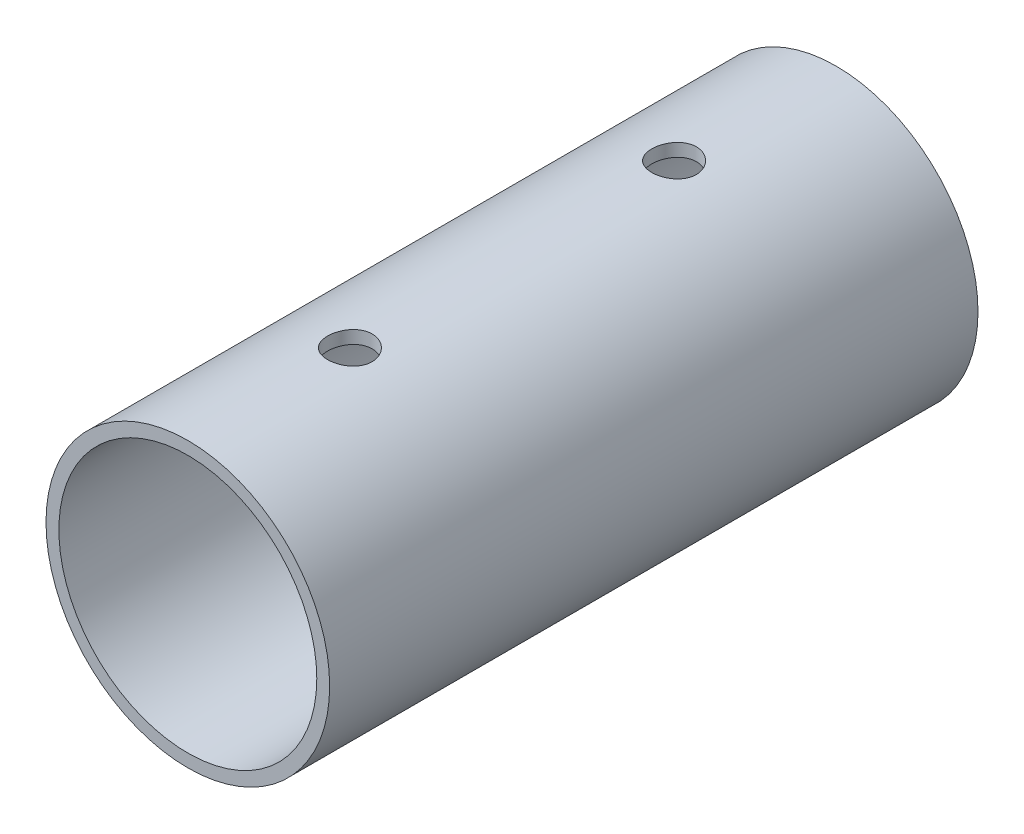
SolidWorks part; units mm, degrees
ref_plane "Front Plane" through (0, 0, 0) normal (0, 0, 1) x (1, 0, 0)
ref_plane "Top Plane" through (0, 0, 0) normal (0, 1, 0) x (1, 0, 0)
ref_plane "Right Plane" through (0, 0, 0) normal (1, 0, 0) x (0, 0, -1)
sketch "Sketch1" plane through (0, 0, 0) normal (0, 0, 1) x (1, 0, 0)
  circle A0 centre (0, 0) radius 15.9125
  circle A1 centre (0, 0) radius 17.5
  dimension "D1" = 35
  dimension "D2" = 31.825
extrude "Boss-Extrude1" add sketch "Sketch1" along normal mid plane 80
sketch "Sketch3" plane through (0, 0, 0) normal (0, 1, 0) x (1, 0, 0)
  line L0 (0, 40) -> (0, 20) construction
  line L1 (17.5, 40) -> (-17.5, 40) construction
  dimension "D1" = 20
hole_wizard "M5 Clearance Hole1" positions "Sketch4" profile "Sketch5" hole size "M5" standard "ANSI Metric"
sketch "Sketch4" plane through (0, 0, 0) normal (0, 1, 0) x (1, 0, 0)
  point P0 (0, 20)
sketch "Sketch5" plane through (0, 0, -20) normal (1, 0, 0) x (0, 0, -1)
  line L0 (0, 0) -> (0, 17.5)
  line L1 (0, 17.5) -> (2.75, 17.5)
  line L2 (2.75, 17.5) -> (2.75, 0)
  line L5 (2.75, 0) -> (0, 0)
  line L11 (0, -6.35) -> (0, 107.95) construction
  dimension "Thru Hole Dia." = 5.5
  dimension "Thru Hole Depth" = 17.5
mirror "Mirror1" about plane through (0, 0, 0) normal (0, 0, 1) of "M5 Clearance Hole1" second plane through (0, 0, 0) second plane normal (0, 1, 0)
equation "\"tubeOutDiameter\" = 35mm"
equation "\"wheelShaftDiameter\"= 12mm"
equation "\"wheelThickness\"= 135mm"
equation "\"BearingDiameter\"= 20mm"
equation "\"BearingThickness\"= 10mm"
equation "\"D1@Sketch1\"=\"tubeOutDiameter\""
equation "\"D2@Sketch1\"=\"tubeOutDiameter\"-0.125in"
